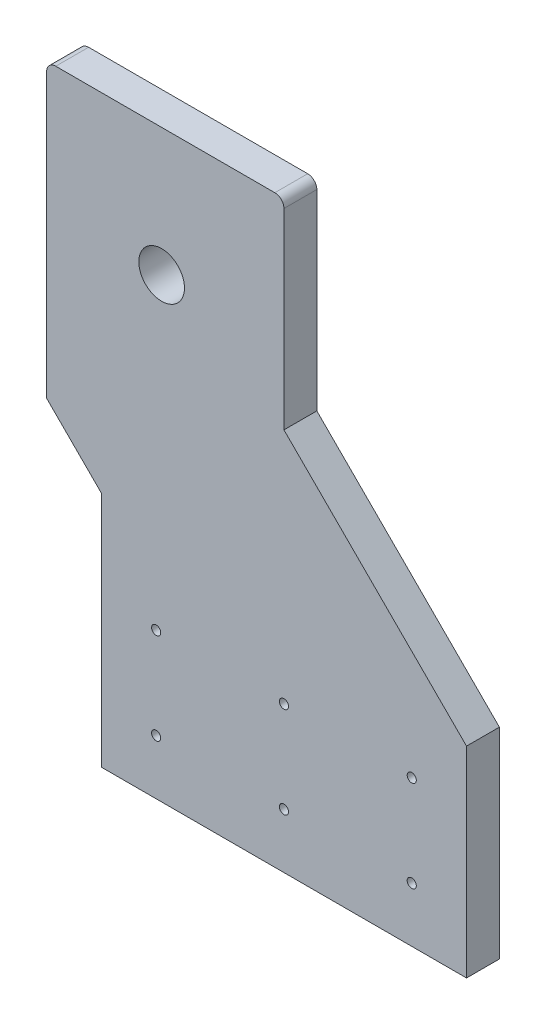
SolidWorks part; units mm, degrees
material "Balsa"
ref_plane "Front Plane" through (0, 0, 0) normal (0, 0, 1) x (1, 0, 0)
ref_plane "Top Plane" through (0, 0, 0) normal (0, 1, 0) x (1, 0, 0)
ref_plane "Right Plane" through (0, 0, 0) normal (1, 0, 0) x (0, 0, -1)
sketch "Sketch1" plane through (0, 0, 0) normal (0, 0, 1) x (1, 0, 0)
  line L0 (4.0702, 148.4877) -> (4.0702, 43.4877)
  line L1 (-95.9298, 153.4877) -> (-0.9298, 153.4877)
  line L2 (-95.9298, -36.5123) -> (-95.9298, -166.5123)
  line L3 (-95.9298, -166.5123) -> (104.0702, -166.5123)
  line L4 (104.0702, -56.5123) -> (104.0702, -166.5123)
  line L5 (-95.9298, 153.4877) -> (104.0702, -166.5123) construction
  line L6 (-95.9298, -166.5123) -> (96.4747, 167.458) construction
  line L7 (4.0702, 43.4877) -> (104.0702, -56.5123)
  line L8 (-95.9298, 153.4877) -> (-120.9298, 153.4877)
  line L9 (-125.9298, 148.4877) -> (-125.9298, -6.5123)
  line L10 (-125.9298, -6.5123) -> (-95.9298, -36.5123)
  circle A0 centre (-62.9298, 83.4877) radius 12.5
  arc A1 (-120.9298, 153.4877) -> (-125.9298, 148.4877) centre (-120.9298, 148.4877) ccw
  arc A2 (4.0702, 148.4877) -> (-0.9298, 153.4877) centre (-0.9298, 148.4877) ccw
  point P0 (0, 0)
  point P16 (-125.9298, 153.4877)
  point P19 (4.0702, 153.4877)
  dimension "D3" = 110
  dimension "D6" = 25
  dimension "D7" = 70
  dimension "D8" = 33
  dimension "D9" = 130
  dimension "D10" = 160
  dimension "D11" = 5
  dimension "D1" = 30
  dimension "D2" = 320
  dimension "D4" = 100
  dimension "D5" = 110
  dimension "D29" = 200
extrude "Boss-Extrude1" add sketch "Sketch1" along normal blind 18
hole_wizard "Hole for M5 300® SC Nuts (SP)1" positions "Sketch2" profile "Sketch3" hole size "M5x0.8" standard "PEM® Metric" end condition through all
sketch "Sketch2" plane through (0, 0, 18) normal (0, 0, 1) x (1, 0, 0)
  line L0 (-95.9298, -166.5123) -> (104.0702, -166.5123) construction
  line L1 (-95.9298, -36.5123) -> (-95.9298, -166.5123) construction
  line L2 (104.0702, -166.5123) -> (104.0702, -56.5123) construction
  point P0 (74.0702, -86.5123)
  point P2 (74.0702, -136.5123)
  point P4 (4.0702, -136.5123)
  point P6 (-65.9298, -136.5123)
  point P8 (-65.9298, -86.5123)
  point P10 (4.0702, -86.5123)
  point P16 (0, 0)
  point P17 (0, 0)
  point P18 (0, 0)
  point P19 (0, 0)
  point P20 (0, 0)
  point P21 (0, 0)
  point P22 (0, 0)
  point P23 (0, 0)
  dimension "D1" = 30
  dimension "D2" = 30
  dimension "D3" = 30
  dimension "D4" = 30
  dimension "D5" = 100
sketch "Sketch3" plane through (74.0702, -86.5123, 18) normal (1, 0, 0) x (0, -1, 0)
  line L0 (0, 0) -> (0, 18)
  line L1 (0, 18) -> (2.5, 18)
  line L2 (2.5, 18) -> (2.5, 0)
  line L5 (2.5, 0) -> (0, 0)
  line L11 (0, -6.35) -> (0, 107.95) construction
  dimension "Thru Hole Dia." = 5
  dimension "Thru Hole Depth" = 18
